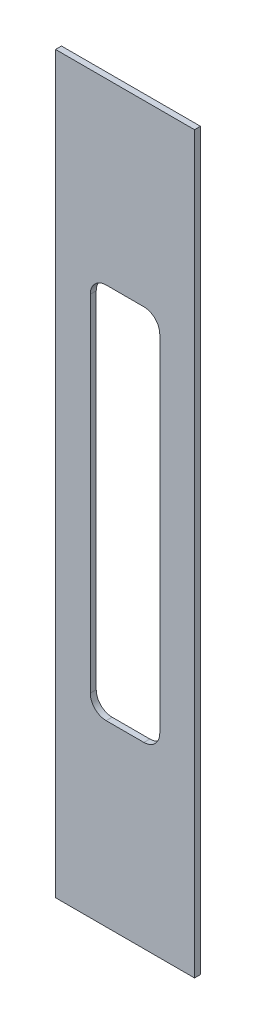
SolidWorks part; units mm, degrees
material "1.4003 (X2CrNi12)"
ref_plane "Płaszczyzna XY" through (0, 0, 0) normal (0, 0, 1) x (1, 0, 0)
ref_plane "Płaszczyzna XZ" through (0, 0, 0) normal (0, 1, 0) x (1, 0, 0)
ref_plane "Płaszczyzna YZ" through (0, 0, 0) normal (1, 0, 0) x (0, 0, -1)
sketch3d "Szkic 3D1"
  line L1 (-40, 217, 113) -> (-140, 217, 113) construction
  line L2 (-40, 217, 113) -> (-40, -217, 113) construction
  line L3 (-40, -217, 113) -> (-140, -217, 113)
  line L4 (-140, 217, 113) -> (-140, -217, 113) construction
  dimension "D1" = 100
  dimension "D2" = 434
ref_plane "Płaszczyzna4" through (0, 0, 113) normal (0, 0, -1) x (-1, 0, 0)
sketch "Szkic3" plane through (0, 0, 113) normal (0, 0, -1) x (-1, 0, 0)
  line L1 (55, 0) -> (-55, 0) construction
  line L3 (130, 185) -> (130, -185)
  line L5 (130, 185) -> (60, 185)
  line L7 (130, -185) -> (60, -185)
  line L8 (60, 185) -> (60, -185)
  dimension "D1" = 370
  dimension "D2" = 185
  dimension "D3" = 70
  dimension "D4" = 60
extrude "Dodanie-wyciągnięcie1" add sketch "Szkic3" against normal mid plane 3
sketch "Szkic4" plane through (0, 0, 114.5) normal (0, 0, 1) x (1, 0, 0)
  line L0 (1.65, 0) -> (-1.65, 0) construction
  line L1 (-60, 185) -> (-60, -185) construction
  line L2 (-85.5, -95) -> (-104.5, -95)
  line L3 (-77.5, -87) -> (-77.5, 87)
  line L4 (-85.5, 95) -> (-104.5, 95)
  line L5 (-112.5, -87) -> (-112.5, 87)
  arc A0 (-104.5, 95) -> (-112.5, 87) centre (-104.5, 87) ccw
  arc A1 (-104.5, -95) -> (-112.5, -87) centre (-104.5, -87) cw
  arc A2 (-85.5, -95) -> (-77.5, -87) centre (-85.5, -87) ccw
  arc A3 (-77.5, 87) -> (-85.5, 95) centre (-85.5, 87) ccw
  point P11 (-112.5, 95)
  point P16 (-77.5, -95)
  point P19 (-77.5, 95)
  dimension "D5" = 8
  dimension "D1" = 95
  dimension "D2" = 35
  dimension "D3" = 17.5
  dimension "D4" = 95
extrude "Wytnij-wyciągnięcie1" cut sketch "Szkic4" against normal up to next
